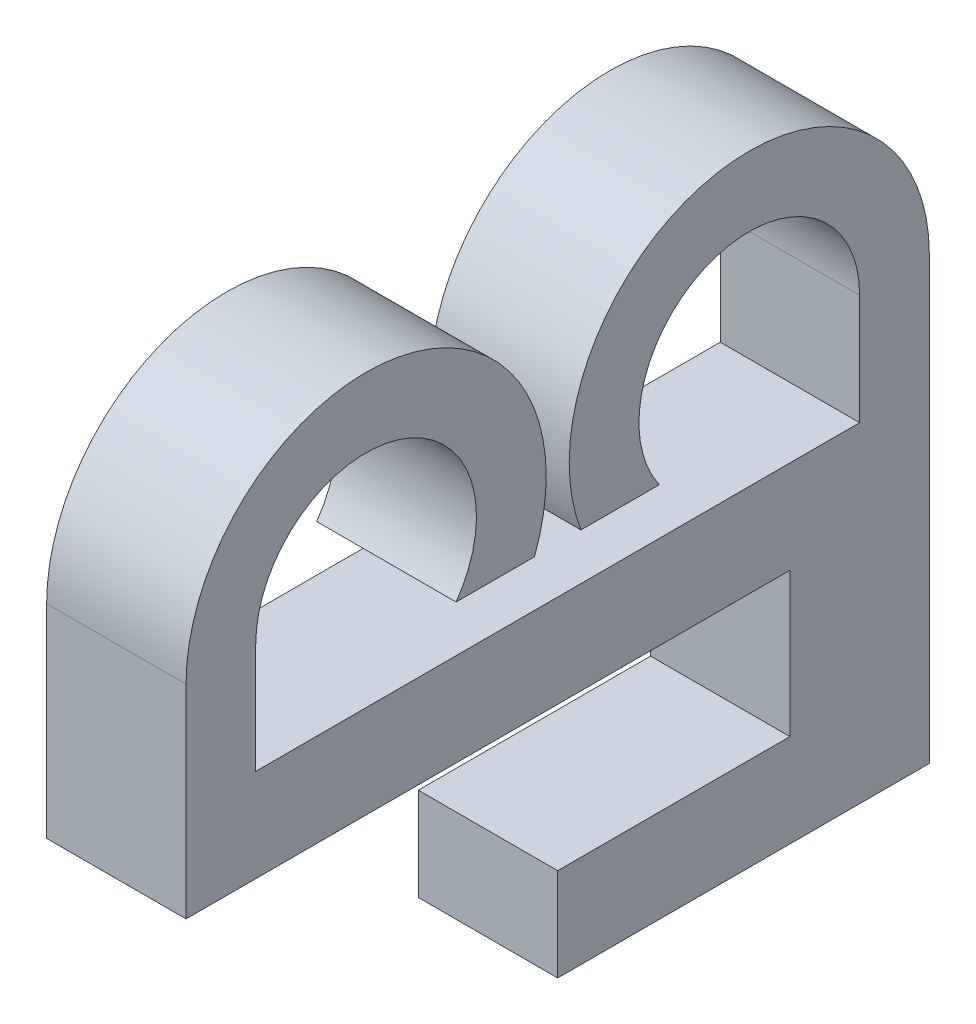
SolidWorks part; units mm, degrees
ref_plane "Front Plane" through (0, 0, 0) normal (0, 0, 1) x (1, 0, 0)
ref_plane "Top Plane" through (0, 0, 0) normal (0, 1, 0) x (1, 0, 0)
ref_plane "Right Plane" through (0, 0, 0) normal (1, 0, 0) x (0, 0, -1)
sketch "Sketch1" plane through (0, 0, 0) normal (1, 0, 0) x (0, 0, -1)
  line L0 (-6.4978, 0) -> (-6.4978, 2.375)
  line L1 (-7.9978, 0) -> (7.9978, 0)
  line L2 (-7.9978, 0) -> (-7.9978, -2)
  line L3 (-7.9978, -2) -> (7.9978, -2)
  line L4 (7.9978, 0) -> (7.9978, -2)
  line L5 (-2.1864, 1) -> (-0.5, 1)
  line L6 (-7.9978, 2.375) -> (-7.9978, 0)
  line L7 (7.9978, 0) -> (7.9978, 2.375)
  line L8 (0.5, 1) -> (2.1864, 1)
  line L9 (6.4978, 2.375) -> (6.4978, 0)
  arc A0 (-6.4978, 2.375) -> (-2.1864, 1) centre (-4.1228, 2.375) cw
  arc A1 (-0.5, 1) -> (-7.9978, 2.375) centre (-4.1228, 2.375) ccw
  arc A2 (7.9978, 2.375) -> (0.5, 1) centre (4.1228, 2.375) ccw
  arc A3 (2.1864, 1) -> (6.4978, 2.375) centre (4.1228, 2.375) cw
  point P4 (0, 0)
  dimension "D4" = 2.375
  dimension "D5" = 1
  dimension "D1" = 2
  dimension "D2" = 1
  dimension "D3" = 1.5
  dimension "D6" = 2.375
extrude "Boss-Extrude1" add sketch "Sketch1" along normal blind 3 contours L5 A1 L6 L1 L0 A0 | L4 L1 L2 L3 | L8 A3 L9 L1 L7 A2
ref_plane "Plane1" through (1.5, 0, 0) normal (1, 0, 0) x (0, 0, -1)
sketch "Sketch2" plane through (0, 0, 0) normal (-1, 0, 0) x (0, 0, 1)
  line L0 (-7.9978, -2) -> (-7.9978, -7.1)
  line L1 (-7.9978, -7.1) -> (0, -7.1)
  line L2 (0, -7.1) -> (0, -5.1)
  line L3 (0, -5.1) -> (-4.9978, -5.1)
  line L4 (-4.9978, -5.1) -> (-4.9978, -2)
  line L5 (7.9978, -2) -> (-7.9978, -2) construction
  line L6 (-4.9978, -2) -> (-7.9978, -2)
  point P3 (0, 0)
  point P10 (0, -2)
  point P11 (-5.6947, -2)
  dimension "D1" = 3.1
  dimension "D2" = 2
  dimension "D3" = 3
extrude "Boss-Extrude2" add sketch "Sketch2" against normal up to surface (3 mm away) up to face at (3, 2.0332, 0)
